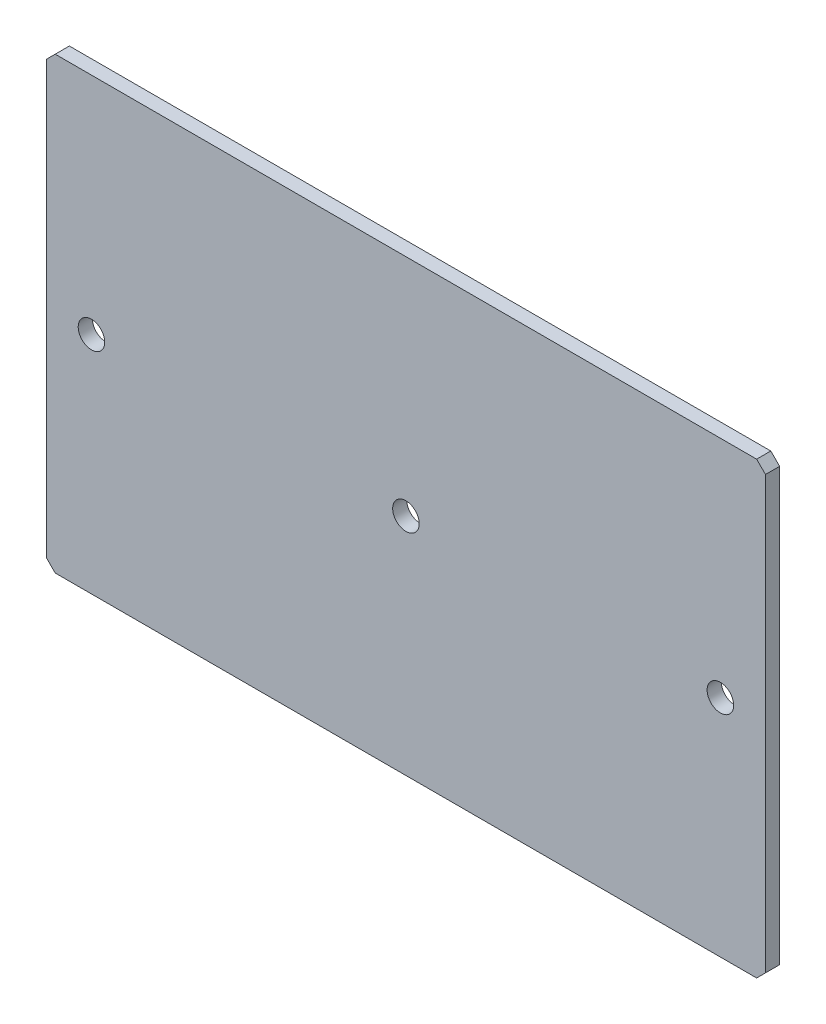
SolidWorks part; units mm, degrees
ref_plane "Front Plane" through (0, 0, 0) normal (0, 0, 1) x (1, 0, 0)
ref_plane "Top Plane" through (0, 0, 0) normal (0, 1, 0) x (1, 0, 0)
ref_plane "Right Plane" through (0, 0, 0) normal (1, 0, 0) x (0, 0, -1)
sketch "Sketch1" plane through (0, 0, 0) normal (0, 0, 1) x (1, 0, 0)
  line L0 (0, 25.4) -> (81.3, 25.4) construction
  line L1 (0, 0) -> (81.3, 0)
  line L2 (0, 0) -> (0, 50.8)
  line L3 (0, 50.8) -> (81.3, 50.8)
  line L4 (81.3, 0) -> (81.3, 50.8)
  circle A0 centre (5.1, 25.4) radius 1.5
  circle A1 centre (40.65, 25.4) radius 1.5
  circle A2 centre (76.2, 25.4) radius 1.5
  point P13 (0, 0)
  point P14 (0, 0)
  point P15 (0, 0)
  dimension "D3" = 3
  dimension "D1" = 81.3
  dimension "D2" = 50.8
  dimension "D4" = 71.1
  dimension "D5" = 5.1
  dimension "D6" = 35.55
extrude "Boss-Extrude1" add sketch "Sketch1" along normal blind 1.6
chamfer "Chamfer1" distance 1 angle 45 4 edges at (81.3, 50.8, 0.8) (81.3, 0, 0.8) (0, 0, 0.8) (0, 50.8, 0.8)
